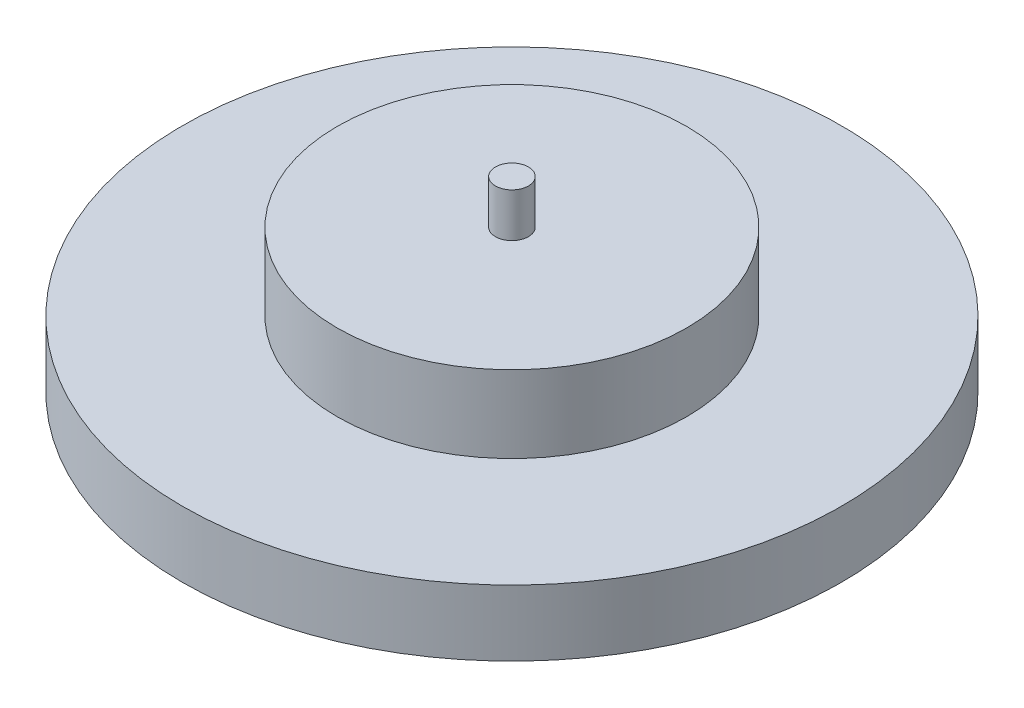
SolidWorks part; units mm, degrees
ref_plane "前视基准面" through (0, 0, 0) normal (0, 0, 1) x (1, 0, 0)
ref_plane "上视基准面" through (0, 0, 0) normal (0, 1, 0) x (1, 0, 0)
ref_plane "右视基准面" through (0, 0, 0) normal (1, 0, 0) x (0, 0, -1)
other "Configuration Table"
sketch "草图1" plane through (0, 0, 0) normal (0, 1, 0) x (1, 0, 0)
  circle A0 centre (0, 0) radius 15
  dimension "D1" = 30
extrude "凸台-拉伸1" add sketch "草图1" along normal blind 3
sketch "草图2" plane through (0, 3, 0) normal (0, 1, 0) x (1, 0, 0)
  circle A0 centre (0, 0) radius 7.95
  dimension "D1" = 15.9
extrude "凸台-拉伸2" add sketch "草图2" along normal blind 3.5
sketch "草图3" plane through (0, 6.5, 0) normal (0, 1, 0) x (1, 0, 0)
  circle A0 centre (0, 0) radius 0.75
  dimension "D1" = 1.5
extrude "凸台-拉伸3" add sketch "草图3" along normal blind 2
